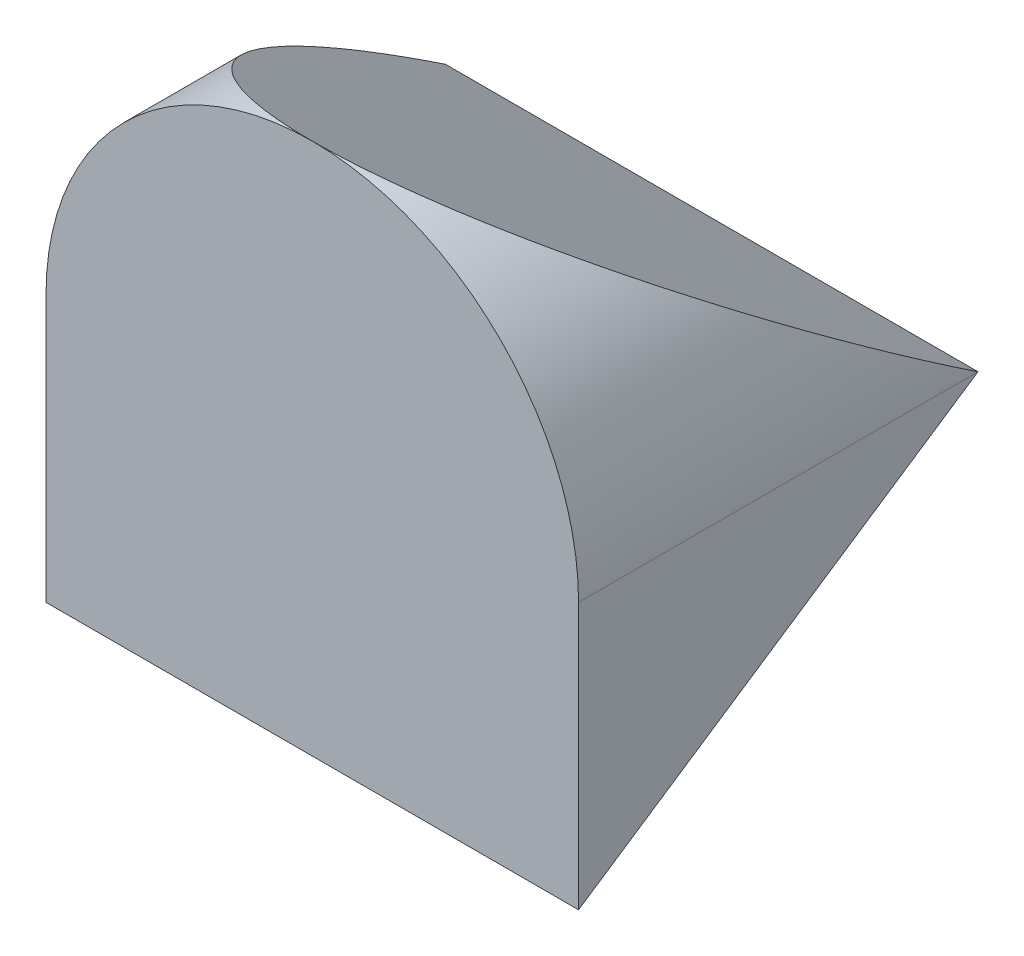
SolidWorks part; units mm, degrees
ref_plane "Front Plane" through (0, 0, 0) normal (0, 0, 1) x (1, 0, 0)
ref_plane "Top Plane" through (0, 0, 0) normal (0, 1, 0) x (1, 0, 0)
ref_plane "Right Plane" through (0, 0, 0) normal (1, 0, 0) x (0, 0, -1)
sketch "Sketch1" plane through (0, 0, 0) normal (0, 0, 1) x (1, 0, 0)
  circle A0 centre (0, 0) radius 10
  dimension "D1" = 20
extrude "Boss-Extrude1" add sketch "Sketch1" along normal blind 15
sketch "Sketch2" plane through (0, 0, 15) normal (0, 0, 1) x (1, 0, 0)
  line L0 (0, 0) -> (10, 0)
  line L1 (0, 0) -> (0, -10)
  circle A0 centre (0, 0) radius 10 construction
  arc A1 (0, -10) -> (10, 0) centre (0, 0) ccw
  circle M1 centre (0, 0) radius 10
extrude "Cut-Extrude1" cut sketch "Sketch2" against normal through all contours L0 L1 M1
ref_plane "Plane1" through (0, 10, 0) normal (0, 1, 0) x (1, 0, 0)
sketch "Sketch3" plane through (0, 10, 0) normal (0, 1, 0) x (1, 0, 0)
  point P0 (0, -14.8602)
ref_plane "Plane2" through (10, 0, 0) normal (1, 0, 0) x (0, 0, -1)
sketch "Sketch5" plane through (10, 0, 0) normal (1, 0, 0) x (0, 0, -1)
  line L0 (0, 0) -> (0, 10)
  line L1 (0, 10) -> (-15, 10)
  line L2 (-15, 10) -> (0, 0)
  dimension "D1" = 10
  dimension "D2" = 15
extrude "Cut-Extrude2" cut sketch "Sketch5" against normal blind 10
sketch "Sketch6" plane through (0, 0, 0) normal (1, 0, 0) x (0, 0, -1)
  line L0 (-15, 10) -> (0, 0)
  line L1 (0, 0) -> (0, 10)
  line L2 (0, 10) -> (-15, 10)
extrude "Cut-Extrude3" cut sketch "Sketch6" against normal blind 10
sketch "Sketch7" plane through (0, 0, 0) normal (1, 0, 0) x (0, 0, -1)
  line L1 (0, 0) -> (-15, 0)
  line L2 (0, 0) -> (0, -10)
  line L3 (0, -10) -> (-15, -10)
  line L4 (-15, 0) -> (-15, -10)
extrude "Boss-Extrude2" add sketch "Sketch7" along normal mid plane 20
sketch "Sketch8" plane through (10, 0, 0) normal (1, 0, 0) x (0, 0, -1)
  line L0 (0, 0) -> (-15, -10)
  line L1 (-15, -10) -> (0, -10)
  line L2 (0, -10) -> (0, 0)
extrude "Cut-Extrude4" cut sketch "Sketch8" against normal blind 20
